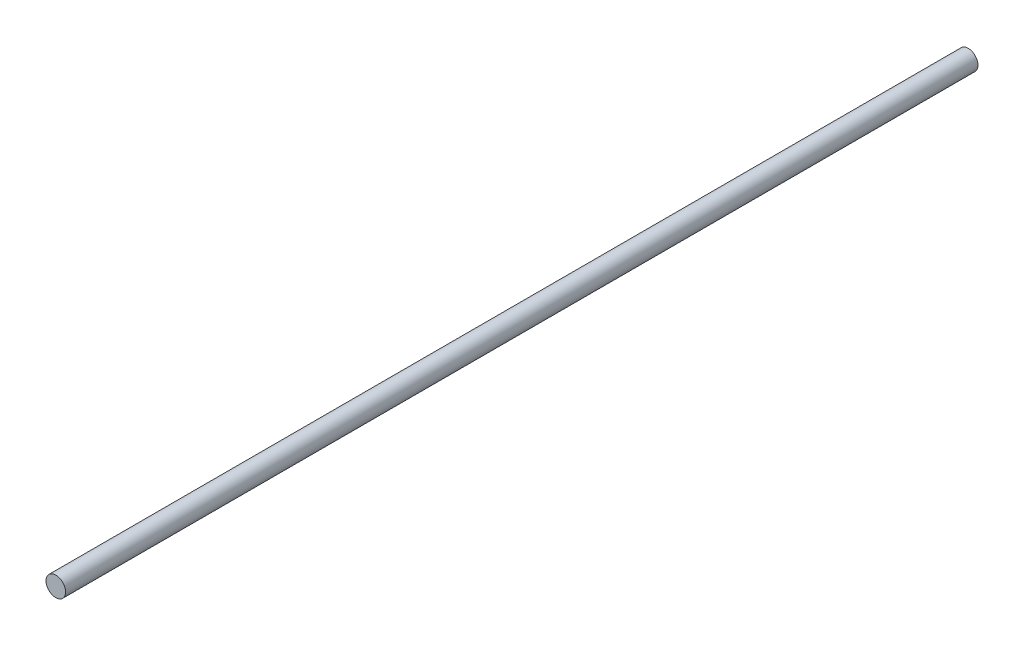
SolidWorks part; units mm, degrees
material "AISI 1045 Aço, trefilado"
ref_plane "Plano frontal" through (0, 0, 0) normal (0, 0, 1) x (1, 0, 0)
ref_plane "Plano superior" through (0, 0, 0) normal (0, 1, 0) x (1, 0, 0)
ref_plane "Plano direito" through (0, 0, 0) normal (1, 0, 0) x (0, 0, -1)
sketch "Esboço1" plane through (0, 0, 0) normal (0, 0, 1) x (1, 0, 0)
  circle A0 centre (0, 0) radius 4
  dimension "D1" = 8
extrude "Ressalto-extrusão1" add sketch "Esboço1" along normal blind 373
